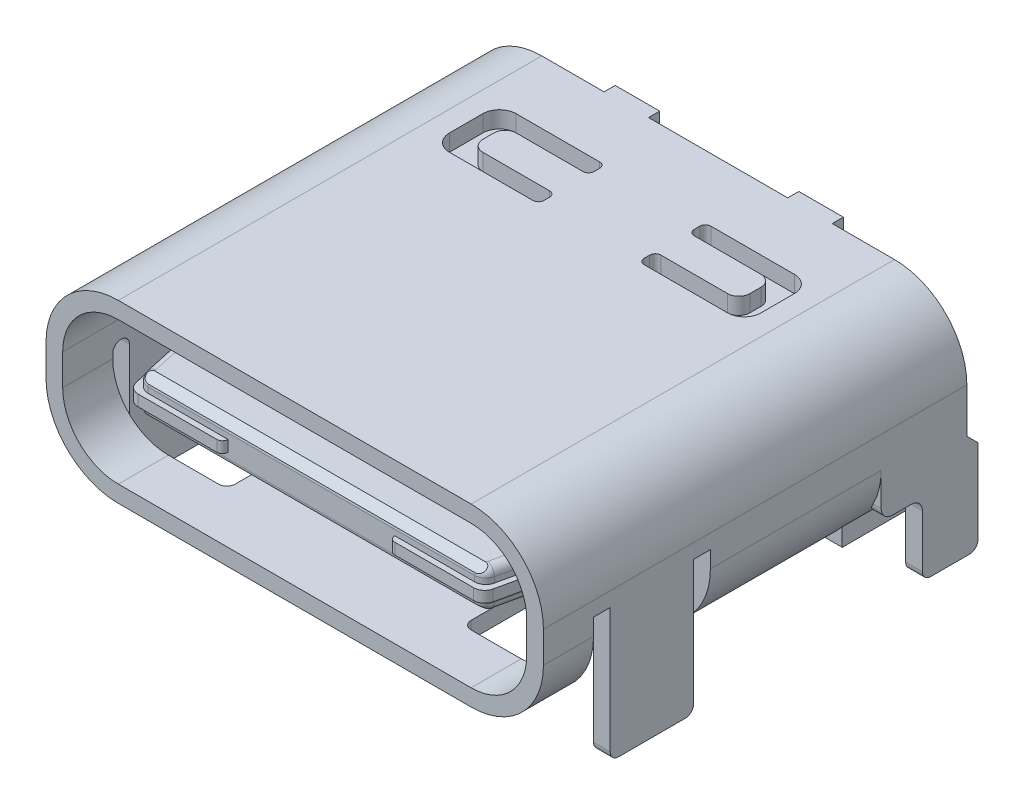
SolidWorks part; units mm, degrees
ref_plane "Płaszczyzna przednia" through (0, 0, 0) normal (0, 0, 1) x (1, 0, 0)
ref_plane "Płaszczyzna górna" through (0, 0, 0) normal (0, 1, 0) x (1, 0, 0)
ref_plane "Płaszczyzna prawa" through (0, 0, 0) normal (1, 0, 0) x (0, 0, -1)
sketch "Sketch1" plane through (0, 0, 0) normal (0, 0, 1) x (1, 0, 0)
  line L0 (-4.47, 0.28) -> (-4.47, -0.28)
  line L1 (-3.17, -1.58) -> (3.17, -1.58)
  line L2 (4.47, -0.28) -> (4.47, 0.28)
  line L3 (3.17, 1.58) -> (-3.17, 1.58)
  arc A0 (-4.47, -0.28) -> (-3.17, -1.58) centre (-3.17, -0.28) ccw
  arc A1 (3.17, -1.58) -> (4.47, -0.28) centre (3.17, -0.28) ccw
  arc A2 (4.47, 0.28) -> (3.17, 1.58) centre (3.17, 0.28) ccw
  arc A3 (-3.17, 1.58) -> (-4.47, 0.28) centre (-3.17, 0.28) ccw
extrude "Boss-Extrude1" add sketch "Sketch1" along normal blind 7.61
sketch "Sketch2" plane through (0, 0, 7.61) normal (0, 0, 1) x (1, 0, 0)
  line L4 (3.17, 1.28) -> (-3.17, 1.28)
  line L5 (-4.17, 0.28) -> (-4.17, -0.28)
  line L6 (-3.17, -1.28) -> (3.17, -1.28)
  line L7 (4.17, -0.28) -> (4.17, 0.28)
  line L8 (-4.47, 0.28) -> (-4.47, -0.28)
  line L9 (-3.17, -1.58) -> (3.17, -1.58)
  line L10 (4.47, -0.28) -> (4.47, 0.28)
  line L11 (3.17, 1.58) -> (-3.17, 1.58)
  line L12 (-4.47, 0.28) -> (-4.47, -0.28)
  line L13 (-3.17, -1.58) -> (3.17, -1.58)
  line L14 (4.47, -0.28) -> (4.47, 0.28)
  line L15 (3.17, 1.58) -> (-3.17, 1.58)
  arc A4 (-3.17, 1.28) -> (-4.17, 0.28) centre (-3.17, 0.28) ccw
  arc A5 (-4.17, -0.28) -> (-3.17, -1.28) centre (-3.17, -0.28) ccw
  arc A6 (3.17, -1.28) -> (4.17, -0.28) centre (3.17, -0.28) ccw
  arc A7 (4.17, 0.28) -> (3.17, 1.28) centre (3.17, 0.28) ccw
  arc A8 (-3.17, 1.58) -> (-4.47, 0.28) centre (-3.17, 0.28) ccw
  arc A9 (-4.47, -0.28) -> (-3.17, -1.58) centre (-3.17, -0.28) ccw
  arc A10 (3.17, -1.58) -> (4.47, -0.28) centre (3.17, -0.28) ccw
  arc A11 (4.47, 0.28) -> (3.17, 1.58) centre (3.17, 0.28) ccw
  arc A12 (-3.17, 1.58) -> (-4.47, 0.28) centre (-3.17, 0.28) ccw
  arc A13 (-4.47, -0.28) -> (-3.17, -1.58) centre (-3.17, -0.28) ccw
  arc A14 (3.17, -1.58) -> (4.47, -0.28) centre (3.17, -0.28) ccw
  arc A15 (4.47, 0.28) -> (3.17, 1.58) centre (3.17, 0.28) ccw
  dimension "D1" = 0
  dimension "D2" = 0.3
extrude "Cut-Extrude1" cut sketch "Sketch2" against normal blind 4.7 flip side to cut
sketch "Sketch3" plane through (0, 1.58, 0) normal (0, 1, 0) x (1, 0, 0)
  line L0 (1.25, 0) -> (-1.25, 0)
  line L1 (0.9, -2.13) -> (0.9, -2.23)
  line L2 (1, -2.33) -> (2.5, -2.33)
  line L3 (2.8, -2.03) -> (2.8, -1.43)
  line L4 (2.5, -1.13) -> (1, -1.13)
  line L5 (0.9, -1.23) -> (0.9, -1.33)
  line L6 (1, -1.43) -> (2.2, -1.43)
  line L7 (2.4, -1.63) -> (2.4, -1.83)
  line L8 (2.2, -2.03) -> (1, -2.03)
  line L9 (-2.8, -1.43) -> (-2.8, -2.03)
  line L10 (-2.5, -2.33) -> (-1, -2.33)
  line L11 (-0.9, -2.23) -> (-0.9, -2.13)
  line L12 (-1, -2.03) -> (-2.2, -2.03)
  line L13 (-2.4, -1.83) -> (-2.4, -1.63)
  line L14 (-2.2, -1.43) -> (-1, -1.43)
  line L15 (-0.9, -1.33) -> (-0.9, -1.23)
  line L16 (-1, -1.13) -> (-2.5, -1.13)
  line L17 (0, 0) -> (0, 0.4904) construction
  arc A0 (0.9, -2.23) -> (1, -2.33) centre (1, -2.23) ccw
  arc A1 (2.5, -2.33) -> (2.8, -2.03) centre (2.5, -2.03) ccw
  arc A2 (2.8, -1.43) -> (2.5, -1.13) centre (2.5, -1.43) ccw
  arc A3 (1, -1.13) -> (0.9, -1.23) centre (1, -1.23) ccw
  arc A4 (0.9, -1.33) -> (1, -1.43) centre (1, -1.33) ccw
  arc A5 (2.4, -1.63) -> (2.2, -1.43) centre (2.2, -1.63) ccw
  arc A6 (2.2, -2.03) -> (2.4, -1.83) centre (2.2, -1.83) ccw
  arc A7 (1, -2.03) -> (0.9, -2.13) centre (1, -2.13) ccw
  arc A8 (-2.5, -1.13) -> (-2.8, -1.43) centre (-2.5, -1.43) ccw
  arc A9 (-2.8, -2.03) -> (-2.5, -2.33) centre (-2.5, -2.03) ccw
  arc A10 (-1, -2.33) -> (-0.9, -2.23) centre (-1, -2.23) ccw
  arc A11 (-0.9, -2.13) -> (-1, -2.03) centre (-1, -2.13) ccw
  arc A12 (-2.4, -1.83) -> (-2.2, -2.03) centre (-2.2, -1.83) ccw
  arc A13 (-2.2, -1.43) -> (-2.4, -1.63) centre (-2.2, -1.63) ccw
  arc A14 (-1, -1.43) -> (-0.9, -1.33) centre (-1, -1.33) ccw
  arc A15 (-0.9, -1.23) -> (-1, -1.13) centre (-1, -1.23) ccw
extrude "Cut-Extrude2" cut sketch "Sketch3" against normal blind 0.3 contours L15 A15 L16 A8 L9 A9 L10 A10 L11 A11 L12 A12 L13 A13 L14 A14 | L4 A3 L5 A4 L6 A5 L7 A6 L8 A7 L1 A0 L2 A1 L3 A2
sketch "Sketch4" plane through (0, 0, 0) normal (0, 0, -1) x (-1, 0, 0)
  line L0 (0, 0.98) -> (0, 1.58) construction
  line L1 (-3.97, 0.48) -> (-3.97, -0.42)
  line L2 (-3.67, -0.72) -> (3.67, -0.72)
  line L3 (3.97, -0.42) -> (3.97, 0.48)
  line L4 (3.47, 0.98) -> (2.05, 0.98)
  line L5 (2.05, 0.98) -> (2.05, 1.58)
  line L6 (2.05, 1.58) -> (1.25, 1.58)
  line L7 (1.25, 1.58) -> (1.25, 0.98)
  line L8 (1.25, 0.98) -> (-1.25, 0.98)
  line L9 (-1.25, 0.98) -> (-1.25, 1.58)
  line L10 (-1.25, 1.58) -> (-2.05, 1.58)
  line L11 (-2.05, 1.58) -> (-2.05, 0.98)
  line L12 (-2.05, 0.98) -> (-3.47, 0.98)
  arc A0 (-3.97, -0.42) -> (-3.67, -0.72) centre (-3.67, -0.42) ccw
  arc A1 (3.67, -0.72) -> (3.97, -0.42) centre (3.67, -0.42) ccw
  arc A2 (3.97, 0.48) -> (3.47, 0.98) centre (3.47, 0.48) ccw
  arc A3 (-3.47, 0.98) -> (-3.97, 0.48) centre (-3.47, 0.48) ccw
extrude "Boss-Extrude2" add sketch "Sketch4" along normal blind 0.2
sketch "Sketch5" plane through (4.47, 0, 0) normal (1, 0, 0) x (0, 0, -1)
  line L0 (-6.41, -0.2) -> (-6.41, -2.23)
  line L1 (-6.26, -2.38) -> (-5.06, -2.38)
  line L2 (-4.91, -2.23) -> (-4.91, -0.2)
  line L3 (-4.61, -0.2) -> (-4.61, -0.28)
  line L4 (-4.61, -0.28) -> (-1.54, -0.28)
  line L5 (-1.54, -0.28) -> (-1.54, -0.88)
  line L6 (-1.34, -1.08) -> (-1, -1.08)
  line L7 (-0.8, -1.28) -> (-0.8, -2.23)
  line L8 (-0.65, -2.38) -> (0.05, -2.38)
  line L9 (0.2, -2.23) -> (0.2, -0.72)
  line L10 (0.2, -0.72) -> (0, -0.52)
  line L11 (0, -0.52) -> (0, 0.28)
  line L12 (-7.61, 0.28) -> (-7.61, -0.28)
  line L13 (-7.61, -0.28) -> (-6.71, -0.28)
  line L14 (-6.71, -0.28) -> (-6.71, -0.2)
  line L15 (-7.61, 0.2097) -> (-7.61, 0.28)
  line L16 (0, 0.28) -> (0, 0.2097)
  line L17 (0, 0.2097) -> (-7.61, 0.2097)
  arc A0 (-6.41, -2.23) -> (-6.26, -2.38) centre (-6.26, -2.23) ccw
  arc A1 (-5.06, -2.38) -> (-4.91, -2.23) centre (-5.06, -2.23) ccw
  arc A2 (-4.61, -0.2) -> (-4.91, -0.2) centre (-4.76, -0.2) ccw
  arc A3 (-1.54, -0.88) -> (-1.34, -1.08) centre (-1.34, -0.88) ccw
  arc A4 (-0.8, -1.28) -> (-1, -1.08) centre (-1, -1.28) ccw
  arc A5 (-0.8, -2.23) -> (-0.65, -2.38) centre (-0.65, -2.23) ccw
  arc A6 (0.05, -2.38) -> (0.2, -2.23) centre (0.05, -2.23) ccw
  arc A7 (-6.41, -0.2) -> (-6.71, -0.2) centre (-6.56, -0.2) ccw
  point P34 (-7.61, 1.58)
  line M2 (-7.61, -0.28) -> (0, -0.28)
  line M3 (0, -0.28) -> (0, 0.28)
extrude "Boss-Extrude3" add sketch "Sketch5" against normal blind 0.3 contours L1 A1 L2 L0 A0 M2 | A7 L0 L2 A2 L3 L17 L12 L14 M2 M3 | L8 A6 L9 L10 L11 L5 A3 L6 A4 L7 A5 M2
sketch "Sketch6" plane through (0, -1.58, 0) normal (0, -1, 0) x (1, 0, 0)
  line L0 (4.47, 4.61) -> (3.17, 4.61)
  line L1 (2.27, 4.61) -> (3.17, 4.61)
  line L2 (2.12, 4.76) -> (2.12, 6.56)
  line L3 (2.27, 6.71) -> (3.17, 6.71)
  line L4 (3.17, 6.71) -> (4.47, 6.71)
  line L5 (-3.17, 4.61) -> (-4.47, 4.61)
  line L6 (-3.17, 4.61) -> (-2.27, 4.61)
  line L7 (-3.17, 6.71) -> (-2.27, 6.71)
  line L8 (-2.12, 6.56) -> (-2.12, 4.76)
  line L9 (-4.47, 6.71) -> (-3.17, 6.71)
  line L10 (-2.12, 5.66) -> (2.12, 5.66) construction
  line L11 (0, 5.66) -> (0, 7.61) construction
  line L12 (-4.47, 6.71) -> (-4.47, 4.61)
  line L13 (4.47, 6.71) -> (4.47, 6.41)
  line L14 (-3.17, 7.61) -> (3.17, 7.61) construction
  line L15 (4.47, 6.41) -> (4.17, 6.41)
  line L16 (4.47, 6.41) -> (4.17, 6.41) construction
  line L17 (4.17, 6.41) -> (4.17, 4.91)
  line L18 (4.17, 4.91) -> (4.47, 4.91)
  line L19 (4.47, 4.91) -> (4.47, 4.61)
  arc A0 (2.12, 4.76) -> (2.27, 4.61) centre (2.27, 4.76) ccw
  arc A1 (2.27, 6.71) -> (2.12, 6.56) centre (2.27, 6.56) ccw
  arc A2 (-2.27, 4.61) -> (-2.12, 4.76) centre (-2.27, 4.76) ccw
  arc A3 (-2.12, 6.56) -> (-2.27, 6.71) centre (-2.27, 6.56) ccw
  point P24 (0, 7.61)
extrude "Cut-Extrude3" cut sketch "Sketch6" against normal blind 1.6
sketch "Sketch7" plane through (0, -1.58, 0) normal (0, -1, 0) x (1, 0, 0)
  line L0 (0, 0) -> (0, -1.7425) construction
  line L1 (4.17, 0) -> (4.17, 1.94)
  line L2 (-4.17, 0) -> (-4.17, 1.94)
  line L3 (-4.17, 1.94) -> (4.17, 1.94)
  line L4 (-4.17, 0) -> (4.17, 0)
extrude "Cut-Extrude4" cut sketch "Sketch7" against normal blind 0.15
sketch "Sketch8" plane through (0, 0, 0) normal (0, 0, -1) x (-1, 0, 0)
  line L0 (0, -1.58) -> (0, -2.8477) construction
  line L1 (-3.17, -1.58) -> (3.17, -1.58) construction
  line L2 (-3.7762, -1.43) -> (-4.17, -1.43)
  line L3 (-4.17, -2.23) -> (-4.17, -0.72) construction
  line L4 (-4.17, -1.43) -> (-4.17, -1.1107)
  line L5 (4.17, -1.43) -> (4.17, -1.1107)
  line L6 (3.7762, -1.43) -> (4.17, -1.43)
  arc A0 (-4.17, -1.1107) -> (-3.7762, -1.43) centre (-3.17, -0.28) ccw construction
  arc A1 (-4.17, -1.1107) -> (-3.7762, -1.43) centre (-3.17, -0.28) ccw
  arc A2 (4.17, -1.1107) -> (3.7762, -1.43) centre (3.17, -0.28) cw
extrude "Boss-Extrude4" add sketch "Sketch8" against normal up to surface (1.94 mm away) up to face at (0, -1.5235, 1.94)
ref_plane "Plane1" through (0, 0, 0) normal (-1, 0, 0) x (0, 0, 1)
mirror "Mirror1" about plane through (0, 0, 0) normal (-1, 0, 0) of "Boss-Extrude3"
sketch "Sketch9" plane through (0, -1.43, 0) normal (0, -1, 0) x (1, 0, 0)
  line L0 (0, 1.94) -> (0, -0.2) construction
  line L1 (-0.6, 0.05) -> (-0.6, -0.29)
  line L2 (-0.6, -0.29) -> (-0.4, -0.29)
  line L3 (-0.4, -0.29) -> (-0.4, 0.05)
  line L4 (-0.4, 0.05) -> (-0.4, 0.2)
  line L5 (-0.4, 0.2) -> (-0.6, 0.2)
  line L6 (-0.6, 0.2) -> (-0.6, 0.05)
  line L7 (-0.9, 0.05) -> (-0.9, 0.2)
  line L8 (-0.9, 0.2) -> (-1.1, 0.2)
  line L9 (-1.1, 0.2) -> (-1.1, 0.05)
  line L10 (-1.1, 0.05) -> (-1.1, -0.29)
  line L11 (-1.1, -0.29) -> (-0.9, -0.29)
  line L12 (-0.9, -0.29) -> (-0.9, 0.05)
  line L13 (-1.6, 0.05) -> (-1.6, -0.29)
  line L14 (-1.6, -0.29) -> (-1.4, -0.29)
  line L15 (-1.4, -0.29) -> (-1.4, 0.05)
  line L16 (-1.4, 0.05) -> (-1.4, 0.2)
  line L17 (-1.4, 0.2) -> (-1.6, 0.2)
  line L18 (-1.6, 0.2) -> (-1.6, 0.05)
  line L19 (-1.9, 0.05) -> (-1.9, 0.2)
  line L20 (-1.9, 0.2) -> (-2.1, 0.2)
  line L21 (-2.1, 0.2) -> (-2.1, 0.05)
  line L22 (-2.1, 0.05) -> (-2.1, -0.29)
  line L23 (-2.1, -0.29) -> (-1.9, -0.29)
  line L24 (-1.9, -0.29) -> (-1.9, 0.05)
  line L25 (-2.6, 0.05) -> (-2.6, -0.29)
  line L26 (-2.6, -0.29) -> (-2.4, -0.29)
  line L27 (-2.4, -0.29) -> (-2.4, 0.05)
  line L28 (-2.4, 0.05) -> (-2.4, 0.2)
  line L29 (-2.4, 0.2) -> (-2.6, 0.2)
  line L30 (-2.6, 0.2) -> (-2.6, 0.05)
  line L31 (-2.9, 0.05) -> (-2.9, 0.2)
  line L32 (-2.9, 0.2) -> (-3.1, 0.2)
  line L33 (-3.1, 0.2) -> (-3.1, 0.05)
  line L34 (-3.1, 0.05) -> (-3.1, -0.29)
  line L35 (-3.1, -0.29) -> (-2.9, -0.29)
  line L36 (-2.9, -0.29) -> (-2.9, 0.05)
  line L37 (0.6, 0.05) -> (0.6, 0.2)
  line L38 (0.6, 0.2) -> (0.4, 0.2)
  line L39 (0.4, 0.2) -> (0.4, 0.05)
  line L40 (0.4, 0.05) -> (0.4, -0.29)
  line L41 (0.4, -0.29) -> (0.6, -0.29)
  line L42 (0.6, -0.29) -> (0.6, 0.05)
  line L43 (0.9, 0.05) -> (0.9, -0.29)
  line L44 (0.9, -0.29) -> (1.1, -0.29)
  line L45 (1.1, -0.29) -> (1.1, 0.05)
  line L46 (1.1, 0.05) -> (1.1, 0.2)
  line L47 (1.1, 0.2) -> (0.9, 0.2)
  line L48 (0.9, 0.2) -> (0.9, 0.05)
  line L49 (1.6, 0.05) -> (1.6, 0.2)
  line L50 (1.6, 0.2) -> (1.4, 0.2)
  line L51 (1.4, 0.2) -> (1.4, 0.05)
  line L52 (1.4, 0.05) -> (1.4, -0.29)
  line L53 (1.4, -0.29) -> (1.6, -0.29)
  line L54 (1.6, -0.29) -> (1.6, 0.05)
  line L55 (1.9, 0.05) -> (1.9, -0.29)
  line L56 (1.9, -0.29) -> (2.1, -0.29)
  line L57 (2.1, -0.29) -> (2.1, 0.05)
  line L58 (2.1, 0.05) -> (2.1, 0.2)
  line L59 (2.1, 0.2) -> (1.9, 0.2)
  line L60 (1.9, 0.2) -> (1.9, 0.05)
  line L61 (2.6, 0.05) -> (2.6, 0.2)
  line L62 (2.6, 0.2) -> (2.4, 0.2)
  line L63 (2.4, 0.2) -> (2.4, 0.05)
  line L64 (2.4, 0.05) -> (2.4, -0.29)
  line L65 (2.4, -0.29) -> (2.6, -0.29)
  line L66 (2.6, -0.29) -> (2.6, 0.05)
  line L67 (2.9, 0.05) -> (2.9, -0.29)
  line L68 (2.9, -0.29) -> (3.1, -0.29)
  line L69 (3.1, -0.29) -> (3.1, 0.05)
  line L70 (3.1, 0.05) -> (3.1, 0.2)
  line L71 (3.1, 0.2) -> (2.9, 0.2)
  line L72 (2.9, 0.2) -> (2.9, 0.05)
  line L73 (2.65, 1.31) -> (2.65, 1.01)
  line L74 (2.65, 1.01) -> (2.85, 1.01)
  line L75 (2.85, 1.01) -> (2.85, 1.31)
  line L76 (2.85, 1.31) -> (2.85, 1.46)
  line L77 (2.85, 1.46) -> (2.65, 1.46)
  line L78 (2.65, 1.46) -> (2.65, 1.31)
  line L79 (3.45, 1.31) -> (3.45, 1.46)
  line L80 (3.45, 1.46) -> (3.15, 1.46)
  line L81 (3.15, 1.46) -> (3.15, 1.31)
  line L82 (3.15, 1.31) -> (3.15, 1.01)
  line L83 (3.15, 1.01) -> (3.45, 1.01)
  line L84 (3.45, 1.01) -> (3.45, 1.31)
  line L85 (2.15, 1.31) -> (2.15, 1.01)
  line L86 (2.15, 1.01) -> (2.35, 1.01)
  line L87 (2.35, 1.01) -> (2.35, 1.31)
  line L88 (2.35, 1.31) -> (2.35, 1.46)
  line L89 (2.35, 1.46) -> (2.15, 1.46)
  line L90 (2.15, 1.46) -> (2.15, 1.31)
  line L91 (1.85, 1.31) -> (1.85, 1.46)
  line L92 (1.85, 1.46) -> (1.65, 1.46)
  line L93 (1.65, 1.46) -> (1.65, 1.31)
  line L94 (1.65, 1.31) -> (1.65, 1.01)
  line L95 (1.65, 1.01) -> (1.85, 1.01)
  line L96 (1.85, 1.01) -> (1.85, 1.31)
  line L97 (1.15, 1.31) -> (1.15, 1.01)
  line L98 (1.15, 1.01) -> (1.35, 1.01)
  line L99 (1.35, 1.01) -> (1.35, 1.31)
  line L100 (1.35, 1.31) -> (1.35, 1.46)
  line L101 (1.35, 1.46) -> (1.15, 1.46)
  line L102 (1.15, 1.46) -> (1.15, 1.31)
  line L103 (0.85, 1.31) -> (0.85, 1.46)
  line L104 (0.85, 1.46) -> (0.65, 1.46)
  line L105 (0.65, 1.46) -> (0.65, 1.31)
  line L106 (0.65, 1.31) -> (0.65, 1.01)
  line L107 (0.65, 1.01) -> (0.85, 1.01)
  line L108 (0.85, 1.01) -> (0.85, 1.31)
  line L109 (0.15, 1.31) -> (0.15, 1.01)
  line L110 (0.15, 1.01) -> (0.35, 1.01)
  line L111 (0.35, 1.01) -> (0.35, 1.31)
  line L112 (0.35, 1.31) -> (0.35, 1.46)
  line L113 (0.35, 1.46) -> (0.15, 1.46)
  line L114 (0.15, 1.46) -> (0.15, 1.31)
  line L115 (-0.15, 1.31) -> (-0.15, 1.46)
  line L116 (-0.15, 1.46) -> (-0.35, 1.46)
  line L117 (-0.35, 1.46) -> (-0.35, 1.31)
  line L118 (-0.35, 1.31) -> (-0.35, 1.01)
  line L119 (-0.35, 1.01) -> (-0.15, 1.01)
  line L120 (-0.15, 1.01) -> (-0.15, 1.31)
  line L121 (-0.85, 1.31) -> (-0.85, 1.01)
  line L122 (-0.85, 1.01) -> (-0.65, 1.01)
  line L123 (-0.65, 1.01) -> (-0.65, 1.31)
  line L124 (-0.65, 1.31) -> (-0.65, 1.46)
  line L125 (-0.65, 1.46) -> (-0.85, 1.46)
  line L126 (-0.85, 1.46) -> (-0.85, 1.31)
  line L127 (-1.15, 1.31) -> (-1.15, 1.46)
  line L128 (-1.15, 1.46) -> (-1.35, 1.46)
  line L129 (-1.35, 1.46) -> (-1.35, 1.31)
  line L130 (-1.35, 1.31) -> (-1.35, 1.01)
  line L131 (-1.35, 1.01) -> (-1.15, 1.01)
  line L132 (-1.15, 1.01) -> (-1.15, 1.31)
  line L133 (-1.85, 1.31) -> (-1.85, 1.01)
  line L134 (-1.85, 1.01) -> (-1.65, 1.01)
  line L135 (-1.65, 1.01) -> (-1.65, 1.31)
  line L136 (-1.65, 1.31) -> (-1.65, 1.46)
  line L137 (-1.65, 1.46) -> (-1.85, 1.46)
  line L138 (-1.85, 1.46) -> (-1.85, 1.31)
  line L139 (-2.15, 1.31) -> (-2.15, 1.46)
  line L140 (-2.15, 1.46) -> (-2.35, 1.46)
  line L141 (-2.35, 1.46) -> (-2.35, 1.31)
  line L142 (-2.35, 1.31) -> (-2.35, 1.01)
  line L143 (-2.35, 1.01) -> (-2.15, 1.01)
  line L144 (-2.15, 1.01) -> (-2.15, 1.31)
  line L145 (-2.85, 1.31) -> (-2.85, 1.01)
  line L146 (-2.85, 1.01) -> (-2.65, 1.01)
  line L147 (-2.65, 1.01) -> (-2.65, 1.31)
  line L148 (-2.65, 1.31) -> (-2.65, 1.46)
  line L149 (-2.65, 1.46) -> (-2.85, 1.46)
  line L150 (-2.85, 1.46) -> (-2.85, 1.31)
  line L151 (-3.15, 1.31) -> (-3.15, 1.46)
  line L152 (-3.15, 1.46) -> (-3.45, 1.46)
  line L153 (-3.45, 1.46) -> (-3.45, 1.31)
  line L154 (-3.45, 1.31) -> (-3.45, 1.01)
  line L155 (-3.45, 1.01) -> (-3.15, 1.01)
  line L156 (-3.15, 1.01) -> (-3.15, 1.31)
  line L157 (3.67, -0.2) -> (-3.67, -0.2) construction
  point P158 (0, -0.2)
extrude "Boss-Extrude5" add sketch "Sketch9" along normal blind 0.2 separate body
sketch "Sketch10" plane through (-3.1, 0, 0) normal (-1, 0, 0) x (0, 0, 1)
  line L0 (1.01, -1.63) -> (1.3171, -1.63)
  line L1 (1.46, -1.63) -> (1.01, -1.63) construction
  line L2 (1.46, -1.43) -> (1.46, -1.4871)
  line L3 (1.46, -1.63) -> (1.46, -1.43) construction
  line L4 (1.01, -1.63) -> (1.5187, -1.7895)
  line L5 (1.5187, -1.7895) -> (1.579, -1.532)
  line L6 (1.579, -1.532) -> (1.46, -1.43)
  line L7 (-0.29, -1.63) -> (0.1, -1.63)
  line L8 (0.2, -1.63) -> (-0.29, -1.63) construction
  line L9 (0.2, -1.43) -> (0.2, -1.53)
  line L10 (0.2, -1.63) -> (0.2, -1.43) construction
  line L11 (0.2, -1.43) -> (0.4482, -1.7765)
  line L12 (0.4482, -1.7765) -> (0.0399, -1.8068)
  line L13 (0.0399, -1.8068) -> (-0.29, -1.63)
  arc A0 (1.3171, -1.63) -> (1.46, -1.4871) centre (1.3171, -1.4871) ccw
  arc A1 (0.2, -1.53) -> (0.1, -1.63) centre (0.1, -1.53) cw
extrude "Cut-Extrude5" cut sketch "Sketch10" against normal up to surface and the other way up to surface
sketch "Sketch11" plane through (-3.1, 0, 0) normal (-1, 0, 0) x (0, 0, 1)
  line L0 (-0.29, -1.63) -> (0.1, -1.63) construction
  line L1 (0.2, -1.43) -> (0.2, -1.53) construction
  line L2 (0.2, -1.43) -> (0.4482, -1.7765) construction
  line L3 (0.4482, -1.7765) -> (0.0399, -1.8068) construction
  line L4 (0.0399, -1.8068) -> (-0.29, -1.63) construction
  line L5 (-0.29, -1.63) -> (0.1, -1.63)
  line L6 (0.2, -1.43) -> (0.2, -1.53)
  line L7 (0.2, -1.43) -> (0.4482, -1.7765)
  line L8 (0.4482, -1.7765) -> (0.0399, -1.8068)
  line L9 (0.0399, -1.8068) -> (-0.29, -1.63)
  arc A0 (0.1, -1.63) -> (0.2, -1.53) centre (0.1, -1.53) ccw construction
  arc A1 (0.1, -1.63) -> (0.2, -1.53) centre (0.1, -1.53) ccw
extrude "Cut-Extrude6" cut sketch "Sketch11" against normal up to surface (6.2 mm away) up to face at (3.1, -1.53, -0.045)
sketch "Sketch12" plane through (0, 0, 2.91) normal (0, 0, 1) x (1, 0, 0)
  line L0 (0, 0.5) -> (0, 1.58) construction
  line L1 (-3.165, 0.2) -> (-3.165, -0.2)
  line L2 (-2.865, -0.5) -> (2.865, -0.5)
  line L3 (3.165, -0.2) -> (3.165, 0.2)
  line L4 (2.865, 0.5) -> (-2.865, 0.5)
  line L5 (3.17, 1.58) -> (-3.17, 1.58) construction
  arc A0 (-3.165, -0.2) -> (-2.865, -0.5) centre (-2.865, -0.2) ccw
  arc A1 (2.865, -0.5) -> (3.165, -0.2) centre (2.865, -0.2) ccw
  arc A2 (3.165, 0.2) -> (2.865, 0.5) centre (2.865, 0.2) ccw
  arc A3 (-2.865, 0.5) -> (-3.165, 0.2) centre (-2.865, 0.2) ccw
  point P14 (0, 1.58)
extrude "Boss-Extrude6" add sketch "Sketch12" along normal blind 1.62 separate body
ref_plane "Plane2" through (0, 0, 0) normal (0, 1, 0) x (1, 0, 0)
sketch "Sketch13" plane through (0, 0, 0) normal (0, 1, 0) x (1, 0, 0)
  line L0 (3.045, -6.06) -> (3.045, -4.53)
  line L1 (3.205, -6.23) -> (3.085, -6.14)
  line L2 (3.245, -6.61) -> (3.245, -6.31)
  line L3 (3.1297, -7.1532) -> (3.2403, -6.6532)
  line L4 (-2.9344, -7.31) -> (2.9344, -7.31)
  line L5 (-3.2403, -6.6532) -> (-3.1297, -7.1532)
  line L6 (-3.245, -6.31) -> (-3.245, -6.61)
  line L7 (-3.085, -6.14) -> (-3.205, -6.23)
  line L8 (-3.045, -4.53) -> (-3.045, -6.06)
  line L9 (-3.045, -4.53) -> (3.045, -4.53)
  line L10 (2.865, -4.53) -> (-2.865, -4.53) construction
  arc A0 (3.045, -6.06) -> (3.085, -6.14) centre (3.145, -6.06) ccw
  arc A1 (3.2344, -6.2653) -> (3.205, -6.23) centre (3.145, -6.31) ccw
  arc A2 (3.245, -6.31) -> (3.2344, -6.2653) centre (3.145, -6.31) ccw
  arc A3 (3.2403, -6.6532) -> (3.245, -6.61) centre (3.045, -6.61) ccw
  arc A4 (3.0667, -7.26) -> (3.1297, -7.1532) centre (2.9344, -7.11) ccw
  arc A5 (2.9344, -7.31) -> (3.0667, -7.26) centre (2.9344, -7.11) ccw
  arc A6 (-3.0667, -7.26) -> (-2.9344, -7.31) centre (-2.9344, -7.11) ccw
  arc A7 (-3.1297, -7.1532) -> (-3.0667, -7.26) centre (-2.9344, -7.11) ccw
  arc A8 (-3.245, -6.61) -> (-3.2403, -6.6532) centre (-3.045, -6.61) ccw
  arc A9 (-3.205, -6.23) -> (-3.245, -6.31) centre (-3.145, -6.31) ccw
  arc A10 (-3.085, -6.14) -> (-3.045, -6.06) centre (-3.145, -6.06) ccw
  point P29 (0, -4.53)
extrude "Boss-Extrude7" add sketch "Sketch13" along normal mid plane 0.7
sketch "Sketch14" plane through (0, 0, 0) normal (0, 1, 0) x (1, 0, 0)
  line L0 (-3.205, -6.23) -> (-3.085, -6.14)
  line L1 (-3.045, -6.06) -> (-3.045, -4.53)
  line L2 (-3.045, -4.53) -> (-3.0911, -4.53)
  line L3 (-3.0911, -4.53) -> (-3.0911, -5.9695)
  line L4 (-3.1311, -6.0495) -> (-3.305, -6.18)
  line L5 (-3.345, -6.26) -> (-3.345, -6.6209)
  line L6 (-3.3403, -6.6641) -> (-3.21, -7.2532)
  line L7 (-3.0147, -7.41) -> (-1.6, -7.41)
  line L8 (-1.5, -7.31) -> (-2.9344, -7.31)
  line L9 (-3.1297, -7.1532) -> (-3.2403, -6.6532)
  line L10 (-3.245, -6.61) -> (-3.245, -6.31)
  line L11 (3.305, -6.18) -> (3.1311, -6.0495)
  line L12 (3.0911, -5.9695) -> (3.0911, -4.53)
  line L13 (3.0911, -4.53) -> (3.045, -4.53)
  line L14 (3.045, -4.53) -> (3.045, -6.06)
  line L15 (3.085, -6.14) -> (3.205, -6.23)
  line L16 (3.245, -6.31) -> (3.245, -6.61)
  line L17 (3.2403, -6.6532) -> (3.1297, -7.1532)
  line L18 (2.9344, -7.31) -> (1.5, -7.31)
  line L19 (1.6, -7.41) -> (3.0147, -7.41)
  line L20 (3.21, -7.2532) -> (3.3403, -6.6641)
  line L21 (3.345, -6.6209) -> (3.345, -6.26)
  arc A0 (-3.085, -6.14) -> (-3.045, -6.06) centre (-3.145, -6.06) ccw
  arc A1 (-3.1311, -6.0495) -> (-3.0911, -5.9695) centre (-3.1911, -5.9695) ccw
  arc A2 (-3.305, -6.18) -> (-3.345, -6.26) centre (-3.245, -6.26) ccw
  arc A3 (-3.345, -6.6209) -> (-3.3403, -6.6641) centre (-3.145, -6.6209) ccw
  arc A4 (-3.21, -7.2532) -> (-3.0147, -7.41) centre (-3.0147, -7.21) ccw
  arc A5 (-1.6, -7.41) -> (-1.5, -7.31) centre (-1.6, -7.31) ccw
  arc A6 (-3.1297, -7.1532) -> (-2.9344, -7.31) centre (-2.9344, -7.11) ccw
  arc A7 (-3.245, -6.61) -> (-3.2403, -6.6532) centre (-3.045, -6.61) ccw
  arc A8 (-3.205, -6.23) -> (-3.245, -6.31) centre (-3.145, -6.31) ccw
  arc A9 (3.0911, -5.9695) -> (3.1311, -6.0495) centre (3.1911, -5.9695) ccw
  arc A10 (3.045, -6.06) -> (3.085, -6.14) centre (3.145, -6.06) ccw
  arc A11 (3.245, -6.31) -> (3.205, -6.23) centre (3.145, -6.31) ccw
  arc A12 (3.2403, -6.6532) -> (3.245, -6.61) centre (3.045, -6.61) ccw
  arc A13 (2.9344, -7.31) -> (3.1297, -7.1532) centre (2.9344, -7.11) ccw
  arc A14 (1.5, -7.31) -> (1.6, -7.41) centre (1.6, -7.31) ccw
  arc A15 (3.0147, -7.41) -> (3.21, -7.2532) centre (3.0147, -7.21) ccw
  arc A16 (3.3403, -6.6641) -> (3.345, -6.6209) centre (3.145, -6.6209) ccw
  arc A17 (3.345, -6.26) -> (3.305, -6.18) centre (3.245, -6.26) ccw
  point P58 (3.045, -4.53)
extrude "Boss-Extrude8" add sketch "Sketch14" along normal mid plane 0.2 separate body
fillet "Fillet2" radius 0.15 34 edges at (3.045, -0.35, 5.295) (3.0556, -0.35, 6.1047) (3.145, -0.35, 6.185) (3.2344, -0.35, 6.2653) (3.245, -0.35, 6.46) (3.2438, -0.35, 6.6317) (3.185, -0.35, 6.9032) (3.0596, -0.35, 7.2659) (0, -0.35, 7.31) (-3.0596, -0.35, 7.2659) (-3.185, -0.35, 6.9032) (-3.2438, -0.35, 6.6317) (-3.245, -0.35, 6.46) (-3.2344, -0.35, 6.2653) (-3.145, -0.35, 6.185) (-3.0556, -0.35, 6.1047) (3.045, 0.35, 5.295) (3.0556, 0.35, 6.1047) (3.145, 0.35, 6.185) (3.2344, 0.35, 6.2653) (3.245, 0.35, 6.46) (3.2438, 0.35, 6.6317) (3.185, 0.35, 6.9032) (3.0596, 0.35, 7.2659) (0, 0.35, 7.31) (-3.0596, 0.35, 7.2659) (-3.185, 0.35, 6.9032) (-3.2438, 0.35, 6.6317) (-3.245, 0.35, 6.46) (-3.2344, 0.35, 6.2653) (-3.145, 0.35, 6.185) (-3.0556, 0.35, 6.1047) (-3.045, -0.35, 5.295) (-3.045, 0.35, 5.295)
sketch "Sketch15" plane through (4.4921, 0, 0.9936) normal (0.9764, 0, 0.216) x (0.216, 0, -0.9764)
  line L0 (-6.4957, 0.2182) -> (-6.2723, 0.3733)
  line L1 (-6.2723, 0.3733) -> (-6.5237, 0.3733)
  line L2 (-6.5237, 0.3733) -> (-6.4957, 0.2182)
  line L3 (-6.5735, 0) -> (-7.2149, 0) construction
  line L4 (-6.5237, -0.3733) -> (-6.4957, -0.2182)
  line L5 (-6.2723, -0.3733) -> (-6.5237, -0.3733)
  line L6 (-6.4957, -0.2182) -> (-6.2723, -0.3733)
sketch "Sketch16" plane through (4.47, 0, 0) normal (1, 0, 0) x (0, 0, -1)
  line L0 (-7.3633, -0.3733) -> (-7.3361, -0.2182) construction
  line L1 (-7.3361, -0.2182) -> (-7.1179, -0.3733) construction
  line L2 (-7.1179, -0.3733) -> (-7.3633, -0.3733) construction
  line L3 (-7.3633, 0.3733) -> (-7.3361, 0.2182) construction
  line L4 (-7.3361, 0.2182) -> (-7.1179, 0.3733) construction
  line L5 (-7.1179, 0.3733) -> (-7.3633, 0.3733) construction
  line L6 (-7.3633, -0.3733) -> (-7.3361, -0.2182)
  line L7 (-7.3361, -0.2182) -> (-7.1179, -0.3733)
  line L8 (-7.1179, -0.3733) -> (-7.3633, -0.3733)
  line L9 (-7.3633, 0.3733) -> (-7.3361, 0.2182)
  line L10 (-7.3361, 0.2182) -> (-7.1179, 0.3733)
  line L11 (-7.1179, 0.3733) -> (-7.3633, 0.3733)
extrude "Cut-Extrude10" cut sketch "Sketch16" against normal through all
